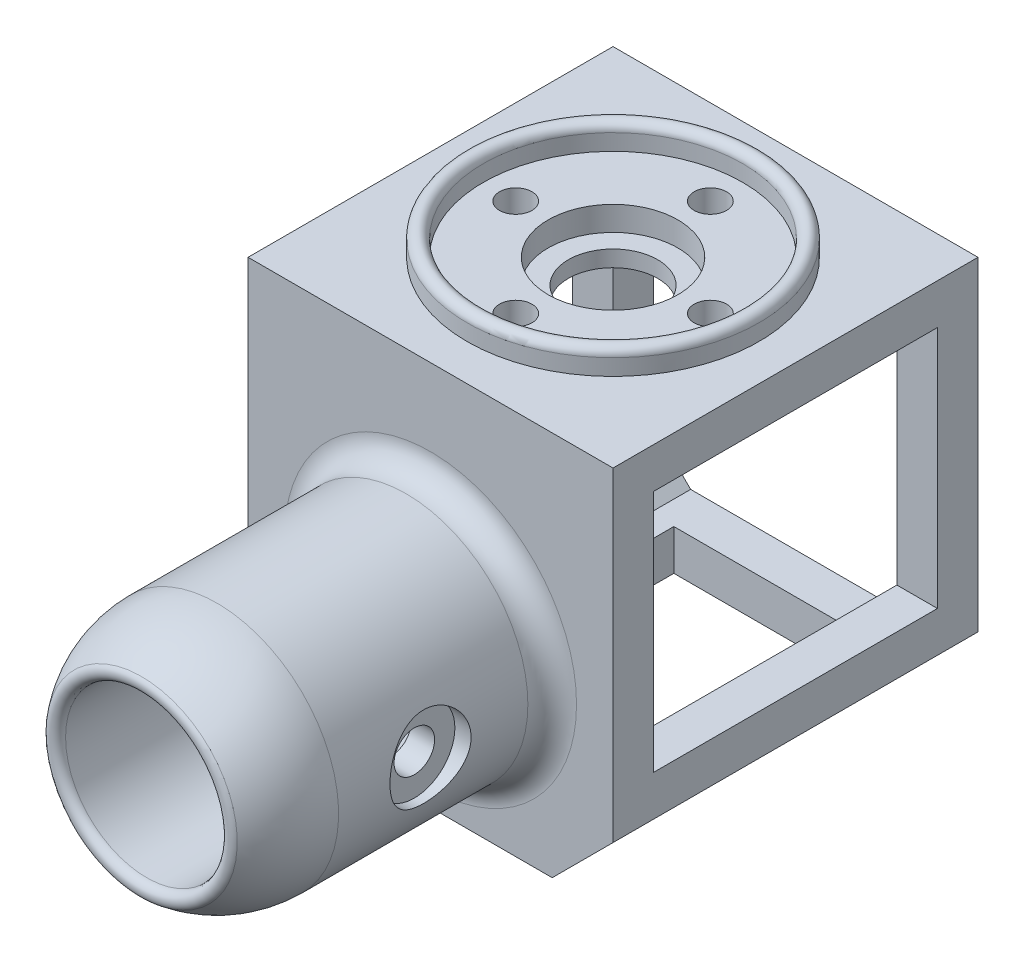
SolidWorks part; units mm, degrees
material "AISI 304"
ref_plane "Front Plane" through (0, 0, 0) normal (0, 0, 1) x (1, 0, 0)
ref_plane "Top Plane" through (0, 0, 0) normal (0, 1, 0) x (1, 0, 0)
ref_plane "Right Plane" through (0, 0, 0) normal (1, 0, 0) x (0, 0, -1)
sketch "Sketch5" plane through (0, 0, 0) normal (0, 0, 1) x (1, 0, 0)
  line L4 (0, 0) -> (0, 61.9057) construction
  line L7 (-15, -20) -> (15, -20)
  line L14 (15, -20) -> (22.5, -12.5)
  line L15 (22.5, -12.5) -> (22.5, 27.5)
  line L16 (22.5, 27.5) -> (-22.5, 27.5)
  line L17 (-22.5, 27.5) -> (-22.5, -12.5)
  line L18 (-22.5, -12.5) -> (-15, -20)
  dimension "D1" = 45
  dimension "D2" = 45
  dimension "D3" = 40
  dimension "D4" = 20
  dimension "D5" = 30
extrude "Boss-Extrude2" add sketch "Sketch5" against normal blind 45
shell "Shell1" thickness 5
sketch "Sketch6" plane through (0, 0, -45) normal (0, 0, -1) x (-1, 0, 0)
  line L13 (12.9289, -15) -> (17.5, -10.4289)
  line L14 (12.9289, -15) -> (17.5, -10.4289)
  line L15 (17.5, -10.4289) -> (17.5, 22.5)
  line L16 (17.5, -10.4289) -> (17.5, 22.5)
  line L17 (17.5, 22.5) -> (-17.5, 22.5)
  line L18 (17.5, 22.5) -> (-17.5, 22.5)
  line L25 (-17.5, 22.5) -> (-17.5, -10.4289)
  line L26 (-17.5, 22.5) -> (-17.5, -10.4289)
  line L27 (-17.5, -10.4289) -> (-12.9289, -15)
  line L28 (-17.5, -10.4289) -> (-12.9289, -15)
  line L29 (-12.9289, -15) -> (12.9289, -15)
  line L30 (-12.9289, -15) -> (12.9289, -15)
  dimension "D1" = 5
extrude "Cut-Extrude1" cut sketch "Sketch6" against normal up to next
sketch "Sketch7" plane through (22.5, 0, 0) normal (1, 0, 0) x (0, 0, -1)
  line L14 (40, 22.5) -> (5, 22.5)
  line L15 (40, -7.5) -> (40, 22.5)
  line L16 (5, 22.5) -> (5, -7.5)
  line L17 (5, -7.5) -> (40, -7.5)
  line L18 (40, 22.5) -> (5, 22.5)
  line L19 (40, -7.5) -> (40, 22.5)
  line L20 (5, 22.5) -> (5, -7.5)
  line L21 (5, -7.5) -> (40, -7.5)
  dimension "D1" = 5
extrude "Cut-Extrude2" cut sketch "Sketch7" against normal through all
sketch "Sketch9" plane through (0, -20, 0) normal (0, -1, 0) x (1, 0, 0)
  line L9 (10, -5) -> (-10, -5)
  line L10 (-10, -5) -> (-10, -40)
  line L11 (-10, -40) -> (10, -40)
  line L12 (10, -40) -> (10, -5)
  line L13 (10, -5) -> (-10, -5)
  line L14 (-10, -5) -> (-10, -40)
  line L15 (-10, -40) -> (10, -40)
  line L16 (10, -40) -> (10, -5)
  dimension "D1" = 5
extrude "Cut-Extrude5" cut sketch "Sketch9" against normal up to next
sketch "Sketch1" plane through (0, 0, 0) normal (1, 0, 0) x (0, 0, -1)
  line L0 (0, 0) -> (-28.8802, 0) construction
  line L1 (0, 10) -> (-35, 10)
  line L3 (-26.3397, 15) -> (0, 15)
  line L4 (0, 15) -> (0, 10)
  arc A0 (-35.6186, 11.7857) -> (-26.3397, 15) centre (-26.3397, 0) cw
  arc A1 (-35, 10) -> (-35.6186, 11.7857) centre (-35, 11) cw
  point P9 (0, 12.5)
  point P13 (-39.5107, 10)
  dimension "D3" = 15
  dimension "D4" = 1
  dimension "D1" = 35
  dimension "D2" = 30
  dimension "D5" = 20
revolve "Revolve1" add sketch "Sketch1" angle 360 about L0
sketch "Sketch10" plane through (0, 0, 0) normal (1, 0, 0) x (0, 0, -1)
  line L0 (38.5, 27.5) -> (38.5, 29.5)
  line L1 (45, 27.5) -> (0, 27.5) construction
  line L2 (40.5, 29.5) -> (40.5, 27.5)
  line L3 (40.5, 27.5) -> (38.5, 27.5)
  line L4 (22.5, 27.5) -> (22.5, 46.5536) construction
  arc A0 (38.5, 29.5) -> (40.5, 29.5) centre (39.5, 29.5) cw
  point P10 (38.5, 34.1458)
  dimension "D3" = 1
  dimension "D1" = 2
  dimension "D2" = 32
revolve "Revolve2" add sketch "Sketch10" angle 360 about L4
hole_wizard "CBORE for M16 Hex Head Bolt1" positions "Sketch18" profile "Sketch19" counterbore size "M16" standard "ANSI Metric"
sketch "Sketch18" plane through (0, 27.5, 0) normal (0, 1, 0) x (1, 0, 0)
  circle A0 centre (0, 22.5) radius 16 construction
  point P0 (0, 22.5)
sketch "Sketch19" plane through (0, 27.5, -22.5) normal (1, 0, 0) x (0, 0, 1)
  line L0 (0, 0) -> (0, 8.3047)
  line L1 (0, 8.3047) -> (5.5, 5)
  line L2 (5.5, 5) -> (5.5, 3)
  line L3 (5.5, 3) -> (8, 3)
  line L4 (8, 3) -> (8, 0)
  line L5 (8, 0) -> (0, 0)
  line L10 (0, 8.3047) -> (-5.5, 5) construction
  line L11 (0, -6.35) -> (0, 107.95) construction
  dimension "Hole Dia." = 11
  dimension "Hole Depth" = 5
  dimension "C'Bore Dia." = 16
  dimension "C'Bore Depth" = 3
  dimension "Drill Angle" = 118
sketch "Sketch11" plane through (0, 27.5, 0) normal (0, 1, 0) x (1, 0, 0)
  circle A1 centre (12, 22.5) radius 2
  circle A2 centre (0, 10.5) radius 2
  circle A3 centre (-12, 22.5) radius 2
  circle A4 centre (0, 34.5) radius 2
  circle A5 centre (0, 22.5) radius 5.5 construction
  point P14 (0, 22.5)
  dimension "D1" = 12
  dimension "D2" = 4
  dimension "D4" = 4
extrude "Cut-Extrude6" cut sketch "Sketch11" against normal up to next
fillet "Fillet1" radius 3 1 edges at (15, 0, 0)
sketch "Sketch15" plane through (0, 0, 0) normal (0, 0, 1) x (1, 0, 0)
  circle A0 centre (0, 0) radius 10
  circle A1 centre (0, 0) radius 10 construction
extrude "Cut-Extrude10" cut sketch "Sketch15" against normal up to next
ref_plane "Plane3" through (15, 0, 0) normal (1, 0, 0) x (0, 0, -1)
hole_wizard "CBORE for M5 Hex Head Bolt1" positions "Sketch16" profile "Sketch17" counterbore size "M5" standard "ANSI Metric" end condition through all
sketch "Sketch16" plane through (15, 0, 0) normal (1, 0, 0) x (0, 0, -1)
  point P0 (-15, 0)
  dimension "D1" = 15
sketch "Sketch17" plane through (15, 0, 15) normal (0, 1, 0) x (0, 0, -1)
  line L0 (0, 0) -> (0, 37.5)
  line L1 (0, 37.5) -> (2.5, 37.5)
  line L3 (2.5, 37.5) -> (2.5, 2)
  line L4 (2.5, 2) -> (5, 2)
  line L5 (5, 2) -> (5, 0)
  line L7 (5, 0) -> (0, 0)
  line L11 (0, -6.35) -> (0, 107.95) construction
  dimension "Thru Hole Dia." = 5
  dimension "Thru Hole Depth" = 37.5
  dimension "C'Bore Dia." = 10
  dimension "C'Bore Depth" = 2
mirror "Mirror1" about plane through (0, 0, 0) normal (1, 0, 0) of "CBORE for M5 Hex Head Bolt1"
